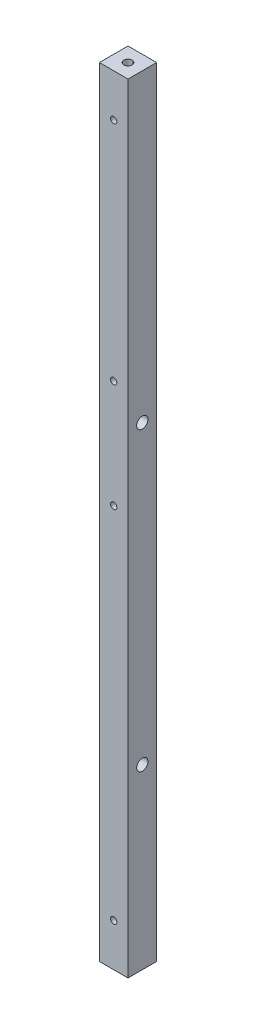
SolidWorks part; units mm, degrees
ref_plane "Plan de face" through (0, 0, 0) normal (0, 0, 1) x (1, 0, 0)
ref_plane "Plan de dessus" through (0, 0, 0) normal (0, 1, 0) x (1, 0, 0)
ref_plane "Plan de droite" through (0, 0, 0) normal (1, 0, 0) x (0, 0, -1)
sketch "Esquisse1" plane through (0, 0, 0) normal (0, 1, 0) x (1, 0, 0)
  line L1 (-5.7, 5.7) -> (5.7, 5.7)
  line L2 (-5.7, 5.7) -> (-5.7, -5.7)
  line L3 (-5.7, -5.7) -> (5.7, -5.7)
  line L4 (5.7, 5.7) -> (5.7, -5.7)
  line L5 (-5.7, 5.7) -> (5.7, -5.7) construction
  line L6 (-5.7, -5.7) -> (5.7, 5.7) construction
  point P0 (0, 0)
  dimension "D1" = 11.4
  dimension "D2" = 11.4
extrude "Boss.-Extru.1" add sketch "Esquisse1" along normal blind 310
sketch "Esquisse2" plane through (0, 0, 5.7) normal (0, 0, 1) x (1, 0, 0)
  line L0 (5.7, 310) -> (5.7, 0) construction
  line L1 (5.7, 310) -> (-5.7, 310) construction
  line L2 (-5.7, 0) -> (5.7, 0) construction
  point P0 (0, 293)
  point P1 (0, 17)
  point P4 (0, 310)
  point P9 (0, 160)
  point P10 (0, 203)
  point P13 (4.3993, 272.7293)
  point P14 (2.142, 247.3617)
  dimension "D1" = 5.7
  dimension "D2" = 5.7
  dimension "D3" = 17
  dimension "D4" = 17
  dimension "D5" = 5.7
  dimension "D6" = 143
  dimension "D7" = 5.7
  dimension "D8" = 90
hole_wizard "Trou taraudé M31" positions "Esquisse4" profile "Esquisse3" tap size "M3" standard "ISO" end condition through all
sketch "Esquisse4" plane through (0, 0, 5.7) normal (0, 0, 1) x (1, 0, 0)
  point P1 (0, 293)
  point P4 (0, 17)
  point P7 (0, 160)
  point P11 (0, 203)
cosmetic thread "Filetage de perçage1" parameters "D2"=3
cosmetic thread "Filetage de perçage2" parameters "D2"=3
sketch "Esquisse3" plane through (0, 293, 5.7) normal (1, 0, 0) x (0, -1, 0)
  line L0 (0, 0) -> (0, 11.4)
  line L1 (0, 11.4) -> (1.25, 11.4)
  line L2 (1.25, 11.4) -> (1.25, 0)
  line L5 (1.25, 0) -> (0, 0)
  line L11 (0, -6.35) -> (0, 107.95) construction
  dimension "Diamètre du trou pour taraudage jusqu'au prochain" = 2.5
  dimension "Profondeur du trou pour taraudage jusqu'au prochain" = 11.4
cosmetic thread "Filetage de perçage5" parameters "D2"=3
cosmetic thread "Filetage de perçage6" parameters "D2"=3
hole_wizard "Trou taraudé M41" positions "Esquisse6" profile "Esquisse5" tap size "M4" standard "ISO"
sketch "Esquisse6" plane through (0, 310, 0) normal (0, 1, 0) x (-1, 0, 0)
  point P1 (0, 0)
sketch "Esquisse5" plane through (0, 310, 0) normal (1, 0, 0) x (0, 0, 1)
  line L0 (0, 0) -> (0, 12.4914)
  line L1 (0, 12.4914) -> (1.65, 11.5)
  line L2 (1.65, 11.5) -> (1.65, 0)
  line L5 (1.65, 0) -> (0, 0)
  line L10 (0, 12.4914) -> (-1.65, 11.5) construction
  line L11 (0, -6.35) -> (0, 107.95) construction
  dimension "Diamètre du trou pour taraudage" = 3.3
  dimension "Profondeur du trou pour taraudage" = 11.5
  dimension "Angle de pointe" = 118
cosmetic thread "Filetage de perçage3" parameters "D1"=8, "D2"=4
hole_wizard "Trou taraudé M42" positions "Esquisse8" profile "Esquisse7" tap size "M4" standard "ISO"
sketch "Esquisse8" plane through (0, 0, 0) normal (0, -1, 0) x (1, 0, 0)
  point P1 (0, 0)
sketch "Esquisse7" plane through (0, 0, 0) normal (1, 0, 0) x (0, 0, -1)
  line L0 (0, 0) -> (0, 12.4914)
  line L1 (0, 12.4914) -> (1.65, 11.5)
  line L2 (1.65, 11.5) -> (1.65, 0)
  line L5 (1.65, 0) -> (0, 0)
  line L10 (0, 12.4914) -> (-1.65, 11.5) construction
  line L11 (0, -6.35) -> (0, 107.95) construction
  dimension "Diamètre du trou pour taraudage" = 3.3
  dimension "Profondeur du trou pour taraudage" = 11.5
  dimension "Angle de pointe" = 118
cosmetic thread "Filetage de perçage4" parameters "D1"=8, "D2"=4
sketch "Esquisse9" plane through (-5.7, 0, 0) normal (-1, 0, 0) x (0, 0, 1)
  line L0 (5.7, 310) -> (5.7, 0) construction
  line L1 (-5.7, 0) -> (5.7, 0) construction
  point P0 (0, 70.7)
  dimension "D1" = 5.7
  dimension "D2" = 70.7
hole_wizard "Dégagement M41" positions "Esquisse11" profile "Esquisse10" hole size "M4" standard "ISO" end condition through all
sketch "Esquisse11" plane through (-5.7, 0, 0) normal (-1, 0, 0) x (0, 0, 1)
  point P4 (0, 70.7)
sketch "Esquisse10" plane through (-5.7, 70.7, 0) normal (0, 1, 0) x (0, 0, 1)
  line L0 (0, 0) -> (0, 11.4)
  line L1 (0, 11.4) -> (2.25, 11.4)
  line L2 (2.25, 11.4) -> (2.25, 0)
  line L5 (2.25, 0) -> (0, 0)
  line L11 (0, -6.35) -> (0, 107.95) construction
  dimension "Diamètre du perçage jusqu'au prochain" = 4.5
  dimension "Profondeur du perçage jusqu'au prochain" = 11.4
sketch "Esquisse12" plane through (-5.7, 0, 0) normal (-1, 0, 0) x (0, 0, 1)
  line L0 (5.7, 310) -> (5.7, 0) construction
  line L1 (-5.7, 0) -> (5.7, 0) construction
  point P0 (0, 188.7)
  dimension "D1" = 5.7
  dimension "D2" = 188.7
hole_wizard "Dégagement M42" positions "Esquisse14" profile "Esquisse13" hole size "M4" standard "ISO" end condition through all
sketch "Esquisse14" plane through (-5.7, 0, 0) normal (-1, 0, 0) x (0, 0, 1)
  point P2 (0, 188.7)
sketch "Esquisse13" plane through (-5.7, 188.7, 0) normal (0, 1, 0) x (0, 0, 1)
  line L0 (0, 0) -> (0, 11.4)
  line L1 (0, 11.4) -> (2.25, 11.4)
  line L2 (2.25, 11.4) -> (2.25, 0)
  line L5 (2.25, 0) -> (0, 0)
  line L11 (0, -6.35) -> (0, 107.95) construction
  dimension "Diamètre du perçage jusqu'au prochain" = 4.5
  dimension "Profondeur du perçage jusqu'au prochain" = 11.4
